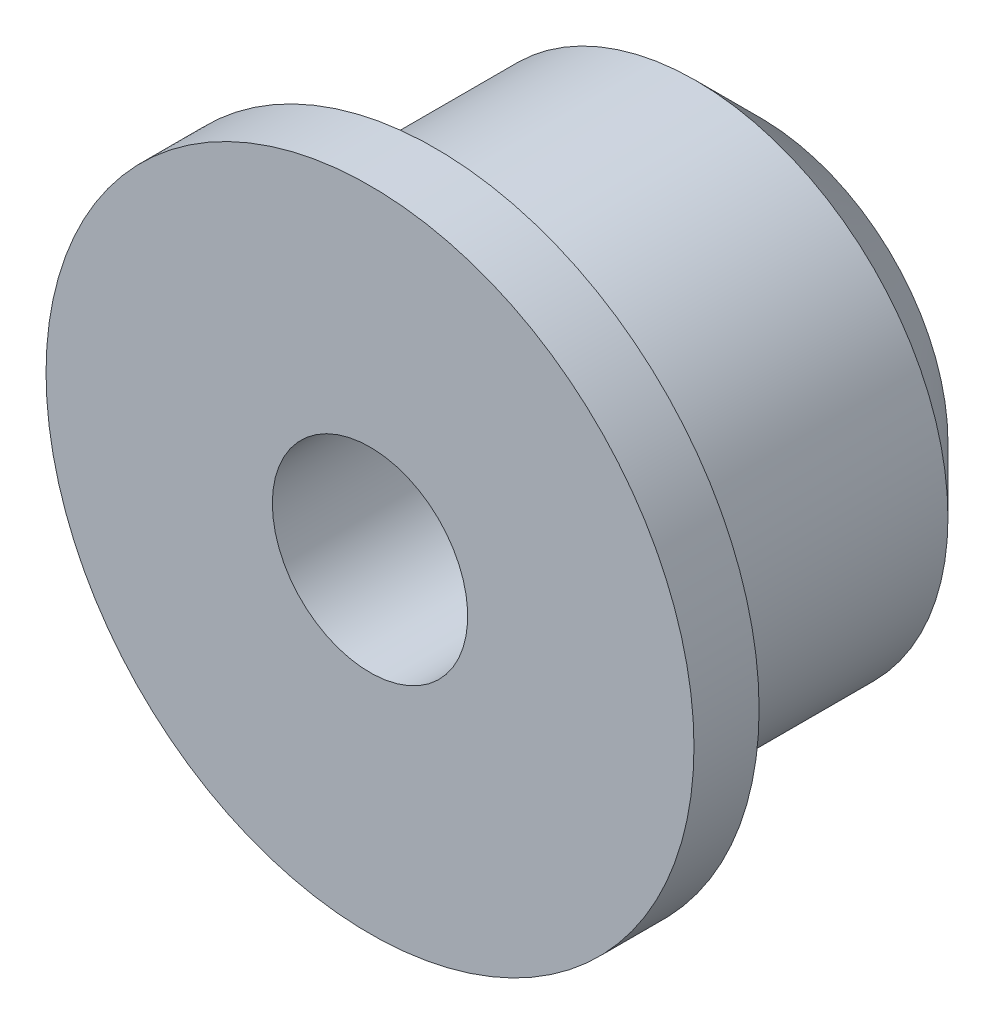
SolidWorks part; units mm, degrees
ref_plane "Front Plane" through (0, 0, 0) normal (0, 0, 1) x (1, 0, 0)
ref_plane "Top Plane" through (0, 0, 0) normal (0, 1, 0) x (1, 0, 0)
ref_plane "Right Plane" through (0, 0, 0) normal (1, 0, 0) x (0, 0, -1)
sketch "Sketch1" plane through (0, 0, 0) normal (0, 0, 1) x (1, 0, 0)
  circle A0 centre (0, 0) radius 7.75
  circle A1 centre (0, 0) radius 2.5
extrude "Boss-Extrude1" add sketch "Sketch1" along normal blind 12
sketch "Sketch2" plane through (0, 0, 12) normal (0, 0, 1) x (1, 0, 0)
  circle A1 centre (0, 0) radius 3
  circle A2 centre (0, 0) radius 9.95
  circle A3 centre (0, 0) radius 9.95
  dimension "D1" = 2.2
extrude "Boss-Extrude2" add sketch "Sketch2" against normal blind 2
chamfer "Chamfer1" distance 2 angle 45 1 edges at (7.75, 0, 0)
sketch "Sketch3" plane through (0, 0, 0) normal (0, 0, -1) x (-1, 0, 0)
  circle A0 centre (0, 0) radius 3
extrude "Cut-Extrude1" cut sketch "Sketch3" against normal through all
